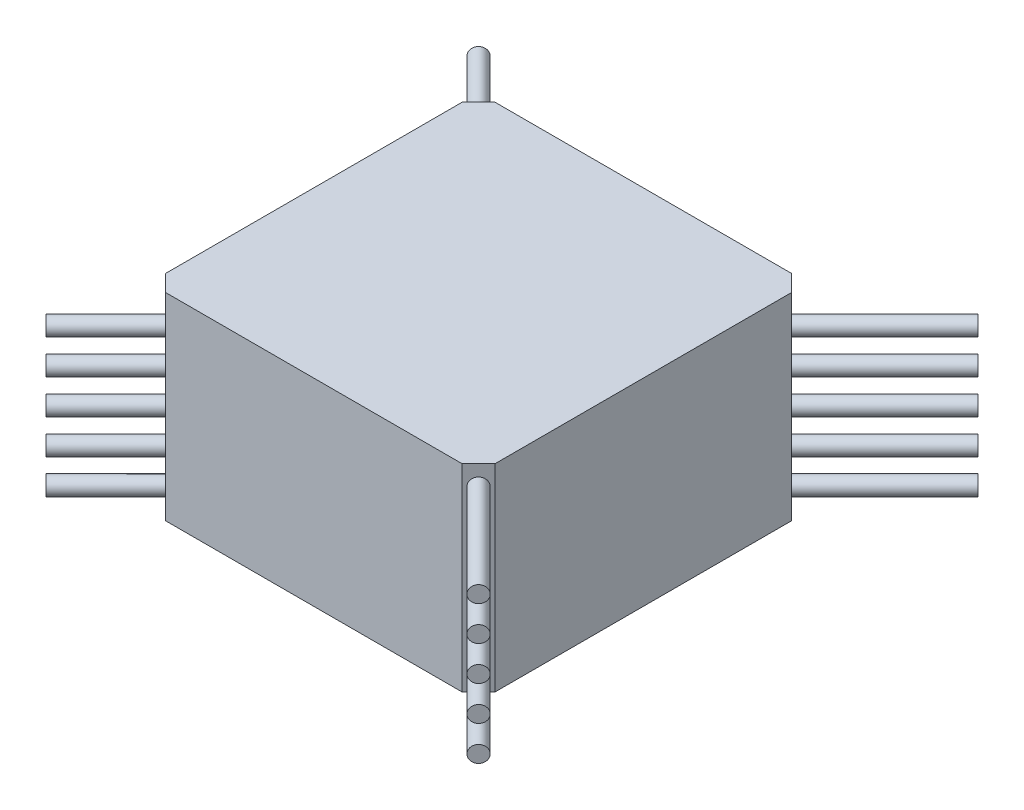
SolidWorks part; units mm, degrees
ref_plane "Front Plane" through (0, 0, 0) normal (0, 0, 1) x (1, 0, 0)
ref_plane "Top Plane" through (0, 0, 0) normal (0, 1, 0) x (1, 0, 0)
ref_plane "Right Plane" through (0, 0, 0) normal (1, 0, 0) x (0, 0, -1)
sketch "Sketch1" plane through (0, 0, 0) normal (0, 1, 0) x (1, 0, 0)
  line L0 (0, -25) -> (0, 25) construction
  line L1 (-22.5, -25) -> (22.5, -25)
  line L2 (-22.5, 25) -> (22.5, 25)
  line L3 (-22.5, 25) -> (-25, 22.5)
  line L4 (25, 22.5) -> (25, -22.5)
  line L5 (22.5, 25) -> (25, 22.5)
  line L6 (-25, -22.5) -> (-22.5, -25)
  line L7 (25, 0) -> (-25, 0) construction
  line L8 (-25, 22.5) -> (-25, -22.5)
  line L9 (22.5, -25) -> (25, -22.5)
  point P1 (0, 0)
  dimension "D1" = 3.5355
  dimension "D3" = 45
extrude "Boss-Extrude1" add sketch "Sketch1" along normal blind 30
sketch "Sketch2" plane through (23.75, 0, 23.75) normal (0.7071, 0, 0.7071) x (0.7071, 0, -0.7071)
  line L0 (0, 30) -> (0, 0) construction
  line L1 (-1.7678, 30) -> (1.7678, 30) construction
  circle A0 centre (0, 27) radius 1.25
  circle A1 centre (0, 21.75) radius 1.25
  circle A2 centre (0, 16.5) radius 1.25
  circle A3 centre (0, 11.25) radius 1.25
  circle A4 centre (0, 6) radius 1.25
  dimension "D1" = 2.5
  dimension "D2" = 3
  dimension "D4" = 5.25
  dimension "D3" = 5
extrude "Boss-Extrude2" add sketch "Sketch2" along normal blind 20 and the other way blind 80 separate body
sketch "Sketch3" plane through (23.75, 0, -23.75) normal (0.7071, 0, -0.7071) x (-0.7071, 0, -0.7071)
  line L0 (0, 30) -> (0, 0) construction
  line L1 (-1.7678, 30) -> (1.7678, 30) construction
  circle A0 centre (0, 24.4) radius 1.25
  circle A1 centre (0, 19.15) radius 1.25
  circle A2 centre (0, 13.9) radius 1.25
  circle A3 centre (0, 8.65) radius 1.25
  circle A4 centre (0, 3.4) radius 1.25
  dimension "D1" = 2.5
  dimension "D2" = 5.6
  dimension "D4" = 5.25
  dimension "D3" = 5
extrude "Boss-Extrude3" add sketch "Sketch3" along normal blind 20 and the other way blind 80 separate body
